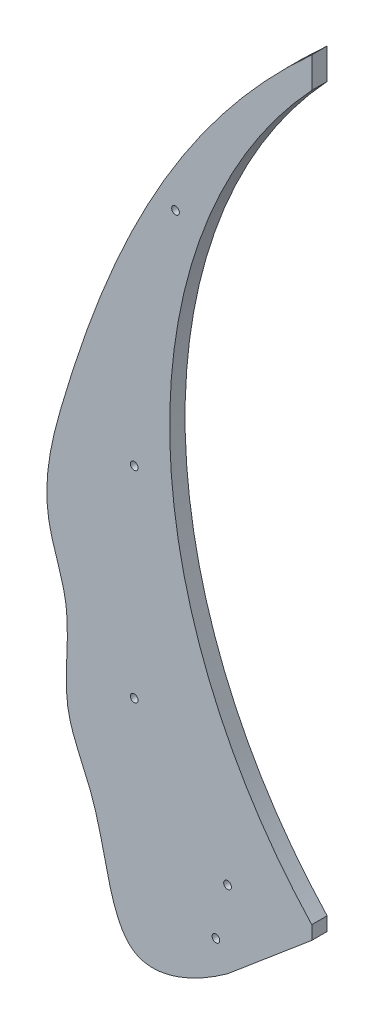
SolidWorks part; units mm, degrees
material "Mahogany"
ref_plane "Front Plane" through (0, 0, 0) normal (0, 0, 1) x (1, 0, 0)
ref_plane "Top Plane" through (0, 0, 0) normal (0, 1, 0) x (1, 0, 0)
ref_plane "Right Plane" through (0, 0, 0) normal (1, 0, 0) x (0, 0, -1)
sketch "Sketch3" plane through (0, 0, 0) normal (0, 0, 1) x (1, 0, 0)
  line L0 (0, 0) -> (-140, 0) construction
  line L1 (-140, 0) -> (-140, -70) construction
  line L3 (0, 490) -> (0, 470)
  line L4 (0, 0) -> (0, 470) construction
  line L5 (0, 0) -> (0, -8.8678)
  line L6 (0, -8.8678) -> (-54.7154, -55)
  arc A0 (0, 0) -> (0, 470) centre (252.5866, 235) cw
  circle A1 centre (-54.7723, -5) radius 2.5
  circle A3 centre (-62.3594, -38.8939) radius 2.5
  circle A4 centre (-115.4957, 69.8074) radius 2.5
  circle A5 centre (-115.4957, 200.7272) radius 2.5
  circle A6 centre (-88.6059, 358.1021) radius 2.5
  spline S0 degree 3 poles (-54.7154, -55) (-77.5, -71.4105) (-130.4378, -93.1255) (-133.7494, -8.3231) (-166.064, 44.0139) (-153.2167, 95.6287) (-178.9784, 151.1562) (-140.6293, 299.759) (-83.9881, 413.7999) (0, 490) knots 0.101497 0.101497 0.101497 0.101497 0.18556 0.290899 0.346089 0.429575 0.479309 0.578896 1 1 1 1
  point P3 (-115.4957, 0)
  point P6 (-54.7154, -55)
  point P9 (-170.5261, -31.8081)
  point P11 (-140, -70)
  point P12 (-140, -70)
  point P13 (0, 0)
  dimension "D5" = 345
  dimension "D6" = 5
  dimension "D12" = 5
  dimension "D1" = 140
  dimension "D2" = 70
  dimension "D3" = 490
  dimension "D4" = 470
  dimension "D8" = 55
  dimension "D9" = 50
extrude "Boss-Extrude1" add sketch "Sketch3" along normal blind 10
